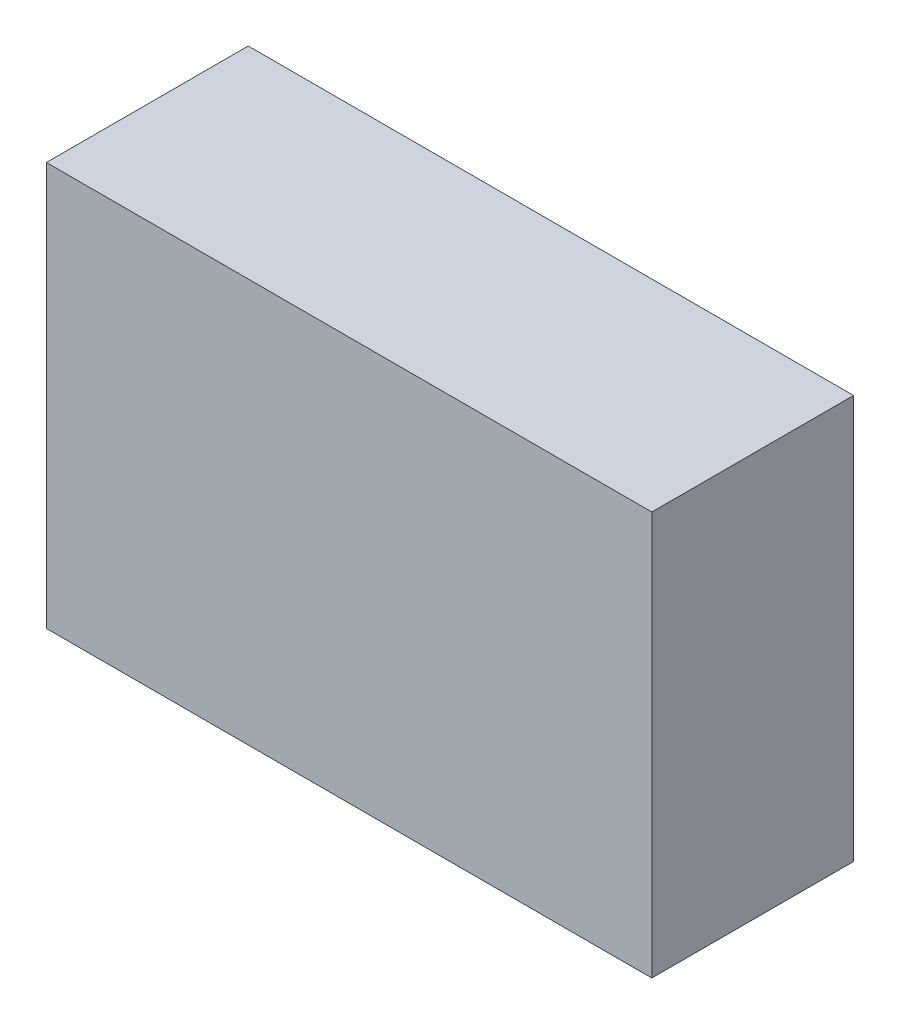
SolidWorks part; units mm, degrees
ref_plane "Front Plane" through (0, 0, 0) normal (0, 0, 1) x (1, 0, 0)
ref_plane "Top Plane" through (0, 0, 0) normal (0, 1, 0) x (1, 0, 0)
ref_plane "Right Plane" through (0, 0, 0) normal (1, 0, 0) x (0, 0, -1)
sketch "Sketch1" plane through (0, 0, 0) normal (0, 0, 1) x (1, 0, 0)
  line L1 (-150, 100) -> (150, 100)
  line L2 (-150, 100) -> (-150, -100)
  line L3 (-150, -100) -> (150, -100)
  line L4 (150, 100) -> (150, -100)
  point P4 (0, 100)
  point P6 (150, 0)
  dimension "D1" = 300
  dimension "D2" = 200
extrude "Extrude1" add sketch "Sketch1" along normal blind 100
